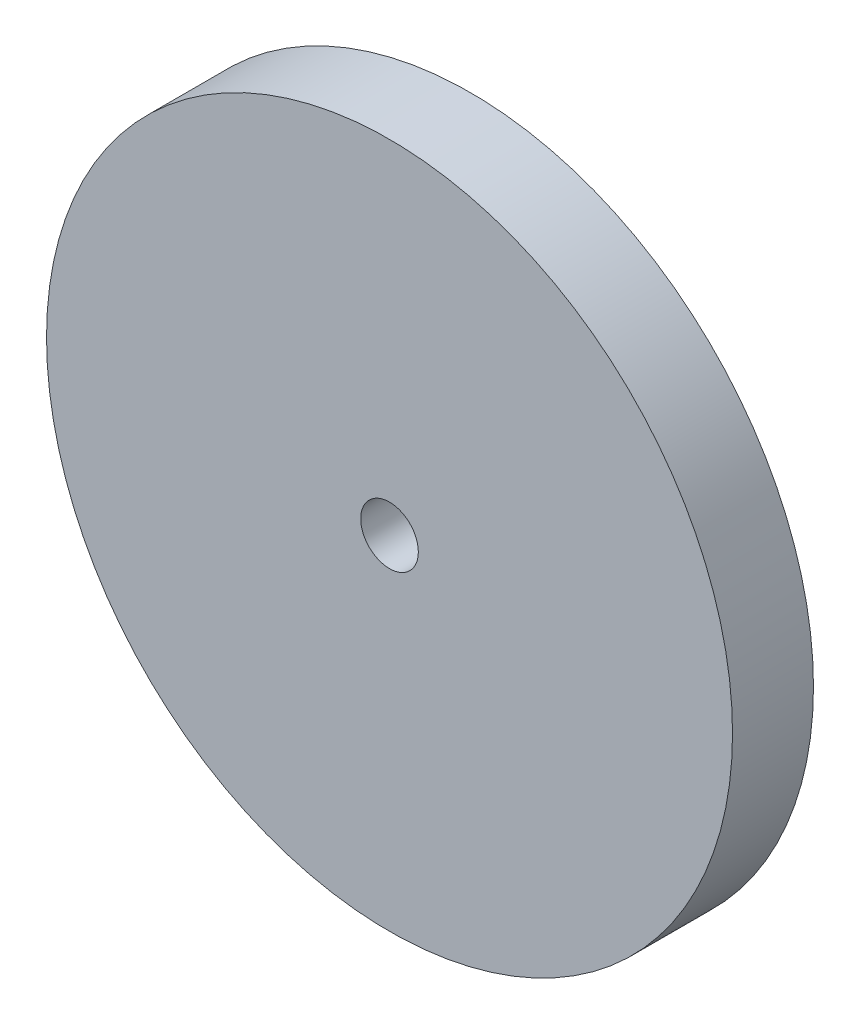
SolidWorks part; units mm, degrees
ref_plane "Front Plane" through (0, 0, 0) normal (0, 0, 1) x (1, 0, 0)
ref_plane "Top Plane" through (0, 0, 0) normal (0, 1, 0) x (1, 0, 0)
ref_plane "Right Plane" through (0, 0, 0) normal (1, 0, 0) x (0, 0, -1)
sketch "Sketch1" plane through (0, 0, 0) normal (0, 0, 1) x (1, 0, 0)
  circle A0 centre (0, 0) radius 25
extrude "Boss-Extrude1" add sketch "Sketch1" along normal blind 5.9
sketch "Sketch2" plane through (0, 0, 5.9) normal (0, 0, 1) x (1, 0, 0)
  circle A0 centre (0, 0) radius 2.1
  point P0 (0, 0)
  dimension "D1" = 4.2
extrude "Cut-Extrude1" cut sketch "Sketch2" against normal up to next
equation "\"e\" = 5.9"
equation "\"D1@Boss-Extrude1\"= \"e\""
